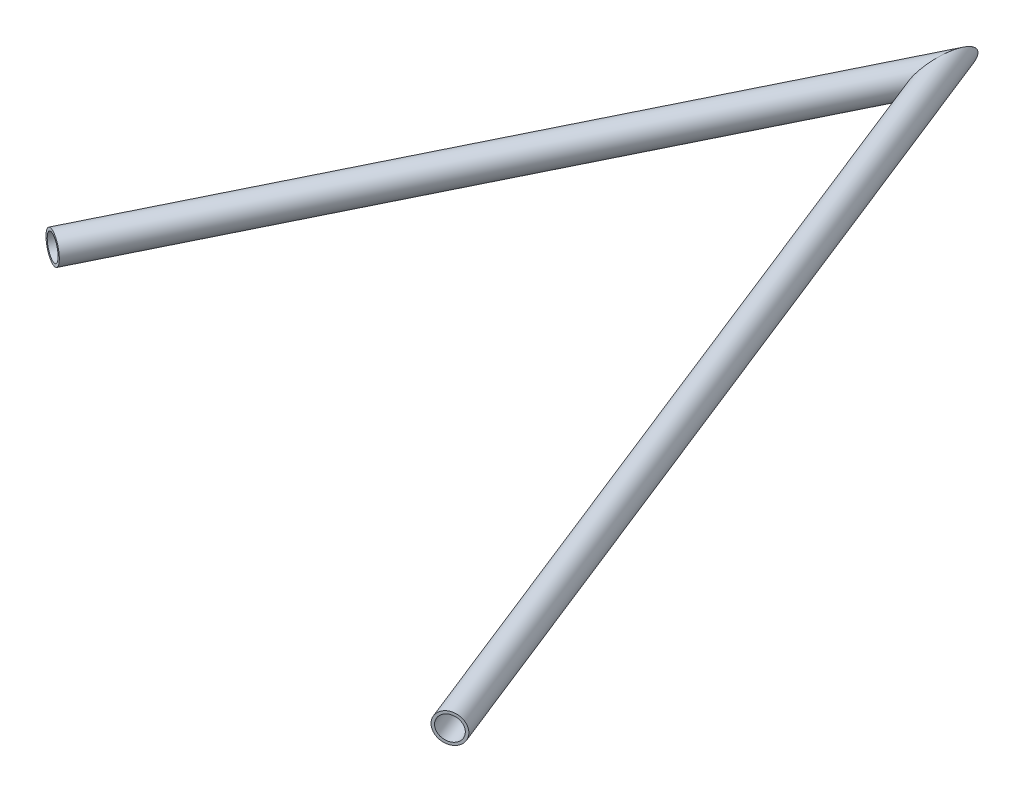
SolidWorks part; units mm, degrees
ref_plane "Front" through (0, 0, 0) normal (0, 0, 1) x (1, 0, 0)
ref_plane "Top" through (0, 0, 0) normal (0, 1, 0) x (1, 0, 0)
ref_plane "Right" through (0, 0, 0) normal (1, 0, 0) x (0, 0, -1)
sketch "Sketch1" plane through (0, 0, 0) normal (0, 1, 0) x (1, 0, 0)
  line L0 (0, 0) -> (-159.428, -324.377)
  line L1 (0, 0) -> (175.642, -442.9906)
  line L2 (214.4851, -456.7409) -> (175.642, -442.9906) construction
  line L3 (175.642, -442.9906) -> (-159.428, -324.377) construction
  line L4 (0, 0) -> (0, -380.814) construction
  circle A0 centre (175.642, -442.9906) radius 14.6812 construction
  circle A1 centre (-159.428, -324.377) radius 14.6812 construction
  point P2 (214.4851, -456.7409)
  dimension "D1" = 29.3624
  dimension "D2" = 29.3624
  dimension "D3" = 355.4449
  dimension "D4" = 361.4384
  dimension "D5" = 476.5404
  dimension "D6" = 169.1225
other "Structural Member1"
ref_plane "Plane1" through (0, 0, 0) normal (-0.4411, 0, 0.8975) x (0.8975, 0, 0.4411)
sketch "Sketch11" plane through (0, 0, 0) normal (-0.4411, 0, 0.8975) x (0.8975, 0, 0.4411)
  circle A0 centre (0, 0) radius 6.4643
  circle A1 centre (0, 0) radius 7.9375
  point P5 (0, 0)
  dimension "D1" = 1.4732
  dimension "D2" = 15.875
sketch3d "3DSketch1"
  line L0 (15.3599, 0, 38.7396) -> (-18.3819, 0, 37.4004)
  line L1 (0, 0, 0) -> (175.642, 0, 442.9906) construction
  line L2 (0, 0, 0) -> (-159.428, 0, 324.377) construction
  line L3 (-1.511, 0, 38.07) -> (-1.511, 33.655, 38.07)
  line L4 (-1.511, 0, 38.07) -> (0, 0, 0)
  dimension "D1" = 38.1
  dimension "D2" = 33.655
